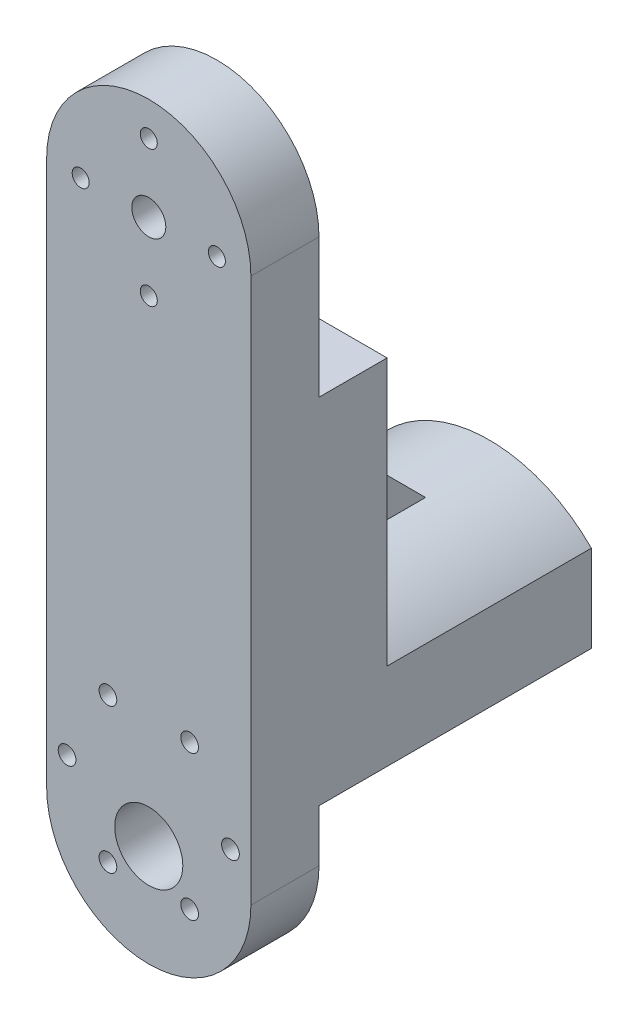
SolidWorks part; units mm, degrees
ref_plane "Front Plane" through (0, 0, 0) normal (0, 0, 1) x (1, 0, 0)
ref_plane "Top Plane" through (0, 0, 0) normal (0, 1, 0) x (1, 0, 0)
ref_plane "Right Plane" through (0, 0, 0) normal (1, 0, 0) x (0, 0, -1)
sketch "Sketch1" plane through (0, 0, 0) normal (0, 0, 1) x (1, 0, 0)
  line L0 (-19.05, 50.8) -> (-19.05, -50.8)
  line L1 (19.05, 50.8) -> (19.05, -50.8)
  line L2 (0, 50.8) -> (0, -50.8) construction
  line L3 (0, 38.1) -> (0, 63.5) construction
  line L4 (-12.7, 50.8) -> (12.7, 50.8) construction
  line L5 (0, -43.18) -> (0, -58.42) construction
  arc A0 (-19.05, 50.8) -> (19.05, 50.8) centre (0, 50.8) cw
  arc A1 (-19.05, -50.8) -> (19.05, -50.8) centre (0, -50.8) ccw
  circle A2 centre (0, 50.8) radius 3.175
  circle A3 centre (0, -50.8) radius 6.35
  circle A4 centre (0, 63.5) radius 1.5875
  circle A5 centre (-12.7, 50.8) radius 1.5875
  circle A6 centre (0, 38.1) radius 1.5875
  circle A7 centre (12.7, 50.8) radius 1.5875
  point P6 (0, 0)
  point P18 (0, 0)
  point P19 (0, 50.8)
  point P21 (0, 50.8)
  point P25 (0, -50.8)
  dimension "D3" = 6.35
  dimension "D4" = 3.175
  dimension "D6" = 12.7
  dimension "D1" = 101.6
  dimension "D2" = 38.1
  dimension "D5" = 12.7
extrude "Boss-Extrude1" add sketch "Sketch1" along normal blind 25.4
sketch "Sketch2" plane through (19.05, 0, 0) normal (1, 0, 0) x (0, 0, -1)
  line L0 (-12.7, 69.85) -> (-12.7, -69.85) construction
  line L1 (0, 69.85) -> (-12.7, 69.85)
  line L2 (0, 69.85) -> (0, 24.892)
  line L3 (0, 24.892) -> (-12.7, 24.892)
  line L4 (-12.7, 69.85) -> (-12.7, 24.892)
  line L5 (0, 69.85) -> (-25.4, 69.85) construction
  line L6 (-25.4, -69.85) -> (0, -69.85) construction
  line L7 (0, -50.8) -> (0, 50.8) construction
  line L12 (0, -24.892) -> (-12.7, -24.892)
  line L13 (0, -24.892) -> (0, -69.85)
  line L14 (0, -69.85) -> (-12.7, -69.85)
  line L15 (-12.7, -24.892) -> (-12.7, -69.85)
  dimension "D1" = 44.958
extrude "Cut-Extrude1" cut sketch "Sketch2" against normal up to next
sketch "Sketch3" plane through (0, 0, 0) normal (0, 0, -1) x (-1, 0, 0)
  line L0 (-15.24, -43.688) -> (15.24, -43.688) construction
  line L1 (-15.24, -43.688) -> (-7.62, -30.1973) construction
  line L2 (15.24, -43.688) -> (7.62, -30.1973) construction
  line L3 (-15.24, -43.688) -> (-7.62, -57.1787) construction
  line L4 (15.24, -43.688) -> (7.62, -57.1787) construction
  line L5 (0, -44.45) -> (0, -57.15) construction
  circle A0 centre (0, -50.8) radius 6.35 construction
  circle A1 centre (-7.62, -30.1973) radius 1.651
  circle A2 centre (-15.24, -43.688) radius 1.651
  circle A3 centre (-7.62, -57.1787) radius 1.651
  circle A4 centre (7.62, -57.1787) radius 1.651
  circle A5 centre (15.24, -43.688) radius 1.651
  circle A6 centre (7.62, -30.1973) radius 1.651
  point P2 (0, -50.8)
  point P7 (44.0119, -37.3126)
  point P14 (0, -43.688)
  dimension "D4" = 3.302
  dimension "D1" = 15.494
  dimension "D2" = 30.988
  dimension "D3" = 30.48
  dimension "D5" = 7.112
extrude "Cut-Extrude2" cut sketch "Sketch3" against normal up to next
sketch "Sketch4" plane through (0, 0, 12.7) normal (0, 0, -1) x (-1, 0, 0)
  line L0 (-15.24, -43.688) -> (15.24, -43.688) construction
  circle A1 centre (0, -43.688) radius 18.5
  dimension "D1" = 37
sketch "Sketch5" plane through (0, 0, 0) normal (0, 0, -1) x (-1, 0, 0)
  line L0 (-15.24, -43.688) -> (15.24, -43.688) construction
  line L1 (-19.05, -24.892) -> (-19.05, -50.8) construction
  line L2 (-19.05, -41.098) -> (-19.05, -24.892)
  line L5 (19.05, 24.892) -> (19.05, -24.892) construction
  line L6 (19.05, -24.892) -> (19.05, -41.148)
  line L7 (19.05, -50.8) -> (19.05, -24.892) construction
  line L8 (19.05, -41.148) -> (18.3248, -41.148)
  line L9 (19.05, -24.892) -> (-19.05, -24.892) construction
  line L10 (19.05, -24.892) -> (-19.05, -24.892) construction
  arc A0 (18.3248, -41.148) -> (-18.3248, -41.148) centre (0, -43.688) ccw
  circle A1 centre (0, -43.688) radius 18.5 construction
  arc A2 (-18.3248, -41.148) -> (-19.05, -41.098) centre (-19.05, -46.3799) ccw
  arc A3 (-19.05, -24.892) -> (19.05, -24.892) centre (0, -43.688) cw
  point P11 (0, 0)
  point P14 (0, 0)
  point P15 (-19.05, -24.892)
  dimension "D1" = 2.54
extrude "Boss-Extrude2" add sketch "Sketch5" along normal blind 38.1
sketch "Sketch6" plane through (0, 0, 0) normal (0, 0, 1) x (1, 0, 0)
  line L0 (-19.05, -24.892) -> (-19.05, -41.148)
  line L1 (-19.05, -41.148) -> (-18.3248, -41.148)
  line L2 (18.3248, -41.148) -> (19.05, -41.098)
  line L3 (19.05, -41.098) -> (19.05, -24.892)
  line L4 (-19.05, -24.892) -> (19.05, -24.892)
  arc A0 (-18.3248, -41.148) -> (18.3248, -41.148) centre (0, -43.688) cw
  point P15 (-19.05, -24.892)
extrude "Boss-Extrude3" add sketch "Sketch6" along normal up to surface (12.7 mm away) up to face at (15.24, -45.339, 12.7)
sketch "Sketch7" plane through (0, 0, 0) normal (1, 0, 0) x (0, 0, -1)
  line L0 (0, -19.4662) -> (0, 5.9338)
  line L1 (0, -24.892) -> (0, -16.9262) construction
  line L2 (0, -24.892) -> (0, 24.892) construction
  line L3 (0, 5.9338) -> (25.4, -19.4662)
  line L5 (0, -19.4662) -> (25.4, -19.4662)
  line L6 (38.1, -16.9262) -> (0, -16.9262) construction
  dimension "D1" = 25.4
  dimension "D2" = 2.54
extrude "Boss-Extrude4" add sketch "Sketch7" along normal mid plane 6.35
